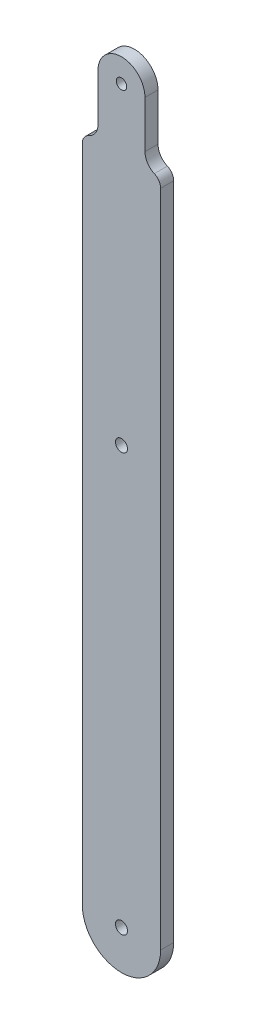
SolidWorks part; units mm, degrees
ref_plane "Front Plane" through (0, 0, 0) normal (0, 0, 1) x (1, 0, 0)
ref_plane "Top Plane" through (0, 0, 0) normal (0, 1, 0) x (1, 0, 0)
ref_plane "Right Plane" through (0, 0, 0) normal (1, 0, 0) x (0, 0, -1)
sketch "Sketch1" plane through (0, 0, 0) normal (0, 0, 1) x (1, 0, 0)
  line L3 (-9.828, 152.4) -> (-9.828, 137.16) construction
  line L4 (-9.828, 137.16) -> (-9.828, 152.4) construction
  line L5 (-9.828, 152.4) -> (-15.543, 152.4) construction
  line L6 (-15.543, 152.4) -> (-9.828, 152.4) construction
  line L7 (-9.828, 152.4) -> (-4.113, 152.4) construction
  line L12 (-19.353, 135.1501) -> (-19.353, -25.4)
  line L13 (-0.303, -25.4) -> (-0.303, 135.1501)
  line L14 (-15.543, 152.4) -> (-15.543, 140.97)
  line L15 (-4.113, 152.4) -> (-4.113, 140.97)
  arc A1 (-19.353, -25.4) -> (-0.303, -25.4) centre (-9.828, -25.4) ccw
  circle A2 centre (-9.828, -25.4) radius 1.4605
  circle A3 centre (-9.828, 152.4) radius 1.27
  arc A4 (-15.543, 152.4) -> (-4.113, 152.4) centre (-9.828, 152.4) cw
  arc A5 (-15.543, 140.97) -> (-17.829, 137.4781) centre (-19.353, 140.97) cw
  arc A6 (-4.113, 140.97) -> (-1.827, 137.4781) centre (-0.303, 140.97) ccw
  arc A7 (-1.827, 137.4781) -> (-0.303, 135.1501) centre (-2.843, 135.1501) cw
  arc A8 (-17.829, 137.4781) -> (-19.353, 135.1501) centre (-16.813, 135.1501) ccw
  dimension "D2" = 2.54
  dimension "D3" = 2.921
  dimension "D8" = 2.54
  dimension "D1" = 11.43
  dimension "D4" = 11.43
  dimension "D5" = 5.715
  dimension "D6" = 5.715
  dimension "D7" = 15.24
  dimension "D9" = 160.5501
extrude "Boss-Extrude1" add sketch "Sketch1" along normal blind 3.175
sketch "Sketch3" plane through (0, 0, 3.175) normal (0, 0, 1) x (1, 0, 0)
  line L0 (-9.828, -25.4) -> (-9.828, 76.2) construction
  circle A0 centre (-9.828, 76.2) radius 1.4605
extrude "Cut-Extrude2" cut sketch "Sketch3" against normal blind 3.175
